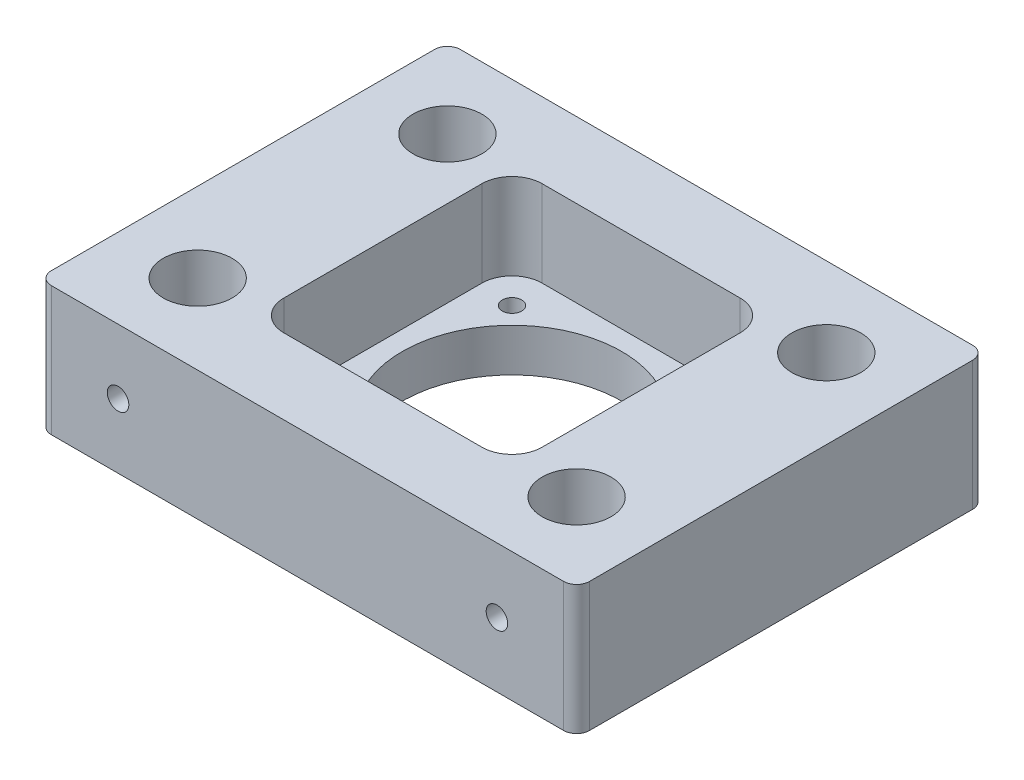
SolidWorks part; units mm, degrees
ref_plane "Front" through (0, 0, 0) normal (0, 0, 1) x (1, 0, 0)
ref_plane "Top" through (0, 0, 0) normal (0, 1, 0) x (1, 0, 0)
ref_plane "Right" through (0, 0, 0) normal (1, 0, 0) x (0, 0, -1)
sketch "Master Sketch" plane through (0, 0, 0) normal (0, 1, 0) x (1, 0, 0)
  line L1 (-62.5, -47.5) -> (62.5, -47.5) construction
  line L2 (-62.5, -47.5) -> (-62.5, 47.5) construction
  line L3 (-62.5, 47.5) -> (62.5, 47.5) construction
  line L4 (62.5, -47.5) -> (62.5, 47.5) construction
  line L5 (0, 47.5) -> (0, -47.5) construction
  line L6 (-62.5, 0) -> (62.5, 0) construction
  line L7 (-25.5, 10.5) -> (-62.5, 10.5) construction
  line L8 (-25.5, 10.5) -> (-25.5, 47.5) construction
  line L9 (-25.5, 47.5) -> (-62.5, 47.5) construction
  line L10 (-62.5, 10.5) -> (-62.5, 47.5) construction
  line L11 (-44, 47.5) -> (-44, 10.5) construction
  line L12 (-25.5, 29) -> (-62.5, 29) construction
  line L13 (25.5, 10.5) -> (62.5, 10.5) construction
  line L14 (25.5, 10.5) -> (25.5, 47.5) construction
  line L15 (25.5, 47.5) -> (62.5, 47.5) construction
  line L16 (62.5, 10.5) -> (62.5, 47.5) construction
  line L17 (44, 47.5) -> (44, 10.5) construction
  line L18 (25.5, 29) -> (62.5, 29) construction
  line L19 (25.5, -10.5) -> (62.5, -10.5) construction
  line L20 (25.5, -10.5) -> (25.5, -47.5) construction
  line L21 (25.5, -47.5) -> (62.5, -47.5) construction
  line L22 (62.5, -10.5) -> (62.5, -47.5) construction
  line L23 (44, -47.5) -> (44, -10.5) construction
  line L24 (25.5, -29) -> (62.5, -29) construction
  line L25 (-25.5, -10.5) -> (-62.5, -10.5) construction
  line L26 (-25.5, -10.5) -> (-25.5, -47.5) construction
  line L27 (-25.5, -47.5) -> (-62.5, -47.5) construction
  line L28 (-62.5, -10.5) -> (-62.5, -47.5) construction
  line L29 (-44, -47.5) -> (-44, -10.5) construction
  line L30 (-25.5, -29) -> (-62.5, -29) construction
  line L31 (-57.435, 15.565) -> (-30.565, 15.565) construction
  line L32 (-57.435, 15.565) -> (-57.435, 42.435) construction
  line L33 (-57.435, 42.435) -> (-30.565, 42.435) construction
  line L34 (-30.565, 15.565) -> (-30.565, 42.435) construction
  line L35 (-44, 42.435) -> (-44, 15.565) construction
  line L36 (-57.435, 29) -> (-30.565, 29) construction
  line L37 (-57.435, -42.435) -> (-30.565, -42.435) construction
  line L38 (-57.435, -42.435) -> (-57.435, -15.565) construction
  line L39 (-57.435, -15.565) -> (-30.565, -15.565) construction
  line L40 (-30.565, -42.435) -> (-30.565, -15.565) construction
  line L41 (-44, -15.565) -> (-44, -42.435) construction
  line L42 (-57.435, -29) -> (-30.565, -29) construction
  line L43 (30.565, -42.435) -> (57.435, -42.435) construction
  line L44 (30.565, -42.435) -> (30.565, -15.565) construction
  line L45 (30.565, -15.565) -> (57.435, -15.565) construction
  line L46 (57.435, -42.435) -> (57.435, -15.565) construction
  line L47 (44, -15.565) -> (44, -42.435) construction
  line L48 (30.565, -29) -> (57.435, -29) construction
  line L49 (30.565, 15.565) -> (57.435, 15.565) construction
  line L50 (30.565, 15.565) -> (30.565, 42.435) construction
  line L51 (30.565, 42.435) -> (57.435, 42.435) construction
  line L52 (57.435, 15.565) -> (57.435, 42.435) construction
  line L53 (44, 42.435) -> (44, 15.565) construction
  line L54 (30.565, 29) -> (57.435, 29) construction
  line L55 (-23.55, -23.55) -> (23.55, -23.55) construction
  line L56 (-23.55, -23.55) -> (-23.55, 23.55) construction
  line L57 (-23.55, 23.55) -> (23.55, 23.55) construction
  line L58 (23.55, -23.55) -> (23.55, 23.55) construction
  line L59 (0, 23.55) -> (0, -23.55) construction
  line L60 (-23.55, 0) -> (23.55, 0) construction
  circle A0 centre (0, 0) radius 12.5 construction
  circle A1 centre (44, 29) radius 8 construction
  circle A2 centre (44, -29) radius 8 construction
  circle A3 centre (-44, -29) radius 8 construction
  circle A4 centre (-44, 29) radius 8 construction
  point P0 (0, 0)
  dimension "D3" = 25
  dimension "D4" = 16
  dimension "D1" = 125
  dimension "D2" = 95
  dimension "D5" = 37
  dimension "D6" = 38
  dimension "D7" = 47.1
sketch "Sketch2" plane through (0, 0, 0) normal (0, 1, 0) x (1, 0, 0)
  line L0 (25.5, -29) -> (62.5, -29) construction
  line L1 (-62.5, 47.5) -> (62.5, 47.5)
  line L2 (-62.5, 47.5) -> (-62.5, -47.5)
  line L3 (-62.5, -47.5) -> (62.5, -47.5)
  line L4 (62.5, 47.5) -> (62.5, -47.5)
  line L5 (25.5, 29) -> (62.5, 29) construction
  circle A0 centre (-44, 29) radius 8
  circle A1 centre (-44, -29) radius 8
  circle A2 centre (44, -29) radius 8
  circle A3 centre (44, 29) radius 8
  circle A5 centre (-44, 29) radius 8 construction
  circle A6 centre (-44, -29) radius 8 construction
  circle A7 centre (44, -29) radius 8 construction
  circle A8 centre (44, 29) radius 8 construction
extrude "Boss-Extrude1" add sketch "Sketch2" along normal blind 30
sketch "Sketch3" plane through (0, 30, 0) normal (0, 1, 0) x (1, 0, 0)
  line L1 (-30, -30) -> (30, -30)
  line L2 (-30, -30) -> (-30, 30)
  line L3 (-30, 30) -> (30, 30)
  line L4 (30, -30) -> (30, 30)
  line L5 (0, 30) -> (0, -30) construction
  line L6 (-30, 0) -> (30, 0) construction
  point P0 (0, 0)
  dimension "D1" = 60
  dimension "D2" = 60
extrude "Cut-Extrude1" cut sketch "Sketch3" against normal blind 20
sketch "Sketch4" plane through (0, 10, 0) normal (0, 1, 0) x (1, 0, 0)
  line L0 (0, 47.5) -> (0, -47.5) construction
  circle A0 centre (0, 0) radius 25.5
  dimension "D1" = 51
extrude "Cut-Extrude2" cut sketch "Sketch4" against normal through all
fillet "Fillet1" radius 7 4 edges at (30, 20, 30) (-30, 20, 30) (30, 20, -30) (-30, 20, -30)
fillet "Fillet3" radius 3 4 edges at (62.5, 15, -47.5) (62.5, 15, 47.5) (-62.5, 15, 47.5) (-62.5, 15, -47.5)
hole_wizard "M4 Clearance Hole1" positions "Sketch11" profile "Sketch10" hole size "M4" standard "ANSI Metric" end condition through all
sketch "Sketch11" plane through (0, 30, 0) normal (0, 1, 0) x (1, 0, 0)
  point P3 (-22, 22)
  point P5 (22, 22)
  point P7 (22, -22)
  point P9 (-22, -22)
  dimension "D1" = 22
  dimension "D2" = 22
  dimension "D3" = 22
  dimension "D4" = 22
sketch "Sketch10" plane through (-22, 30, -22) normal (1, 0, 0) x (0, 0, 1)
  line L0 (0, 0) -> (0, 30)
  line L1 (0, 30) -> (2.25, 30)
  line L2 (2.25, 30) -> (2.25, 0)
  line L5 (2.25, 0) -> (0, 0)
  line L11 (0, -6.35) -> (0, 107.95) construction
  dimension "Thru Hole Dia." = 4.5
  dimension "Thru Hole Depth" = 30
hole_wizard "M6x1.0 Tapped Hole1" positions "Sketch13" profile "Sketch12" tap size "M6x1.0" standard "ANSI Metric"
sketch "Sketch13" plane through (0, 0, 47.5) normal (0, 0, 1) x (1, 0, 0)
  line L0 (-44, 30) -> (-44, 0) construction
  line L1 (44, 30) -> (44, 0) construction
  point P0 (-44, 15)
  point P4 (44, 15)
sketch "Sketch12" plane through (-44, 15, 47.5) normal (1, 0, 0) x (0, -1, 0)
  line L0 (0, 0) -> (0, 10.5)
  line L1 (0, 10.5) -> (2.5, 10.5)
  line L2 (2.5, 10.5) -> (2.5, 0)
  line L5 (2.5, 0) -> (0, 0)
  line L11 (0, -6.35) -> (0, 107.95) construction
  dimension "Thru Tap Drill Dia." = 5
  dimension "Thru Tap Drill Depth" = 10.5
cosmetic thread "Hole Thread1" parameters "D2"=6
cosmetic thread "Hole Thread2" parameters "D2"=6
hole_wizard "M6x1.0 Tapped Hole2" positions "Sketch15" profile "Sketch14" tap size "M6x1.0" standard "ANSI Metric"
sketch "Sketch15" plane through (0, 0, -47.5) normal (0, 0, -1) x (-1, 0, 0)
  line L0 (44, 30) -> (44, 0) construction
  line L1 (-44, 30) -> (-44, 0) construction
  point P0 (-44, 15)
  point P2 (44, 15)
sketch "Sketch14" plane through (44, 15, -47.5) normal (1, 0, 0) x (0, 1, 0)
  line L0 (0, 0) -> (0, 10.5)
  line L1 (0, 10.5) -> (2.5, 10.5)
  line L2 (2.5, 10.5) -> (2.5, 0)
  line L5 (2.5, 0) -> (0, 0)
  line L11 (0, -6.35) -> (0, 107.95) construction
  dimension "Thru Tap Drill Dia." = 5
  dimension "Thru Tap Drill Depth" = 10.5
cosmetic thread "Hole Thread3" parameters "D2"=6
cosmetic thread "Hole Thread4" parameters "D2"=6
